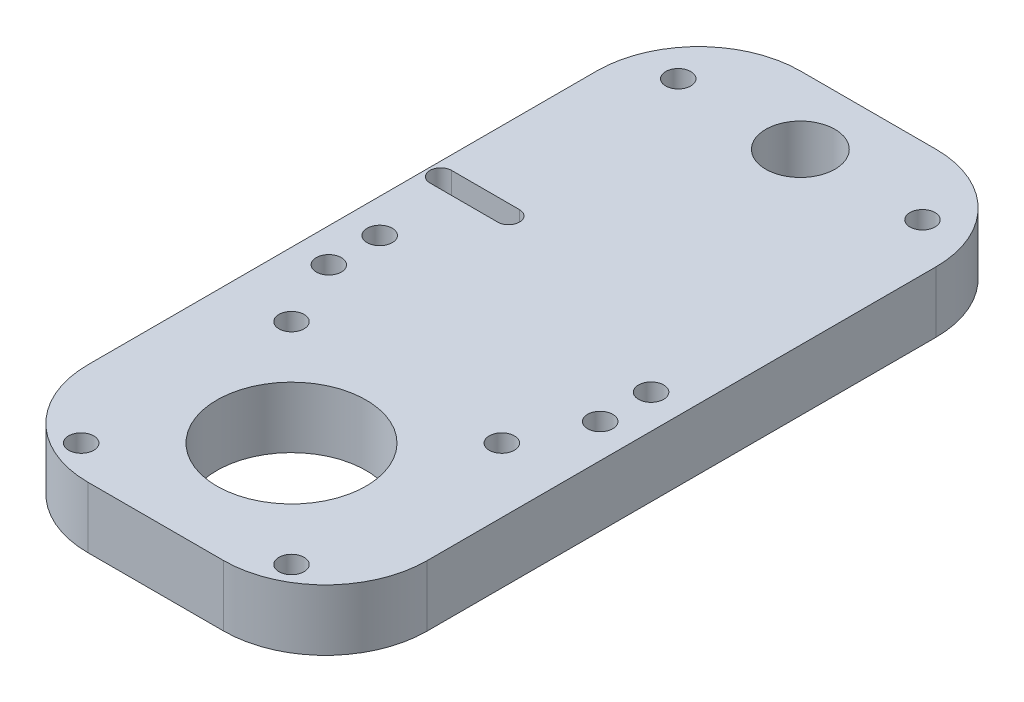
SolidWorks part; units mm, degrees
ref_plane "Front Plane" through (0, 0, 0) normal (0, 0, 1) x (1, 0, 0)
ref_plane "Top Plane" through (0, 0, 0) normal (0, 1, 0) x (1, 0, 0)
ref_plane "Right Plane" through (0, 0, 0) normal (1, 0, 0) x (0, 0, -1)
sketch "Sketch1" plane through (0, 0, 0) normal (0, 1, 0) x (1, 0, 0)
  line L1 (9.489, -12.4157) -> (59.489, -12.4157)
  line L2 (9.489, -12.4157) -> (9.489, 92.5843)
  line L3 (9.489, 92.5843) -> (59.489, 92.5843)
  line L4 (59.489, -12.4157) -> (59.489, 92.5843)
  dimension "D1" = 50
  dimension "D2" = 105
extrude "Boss-Extrude1" add sketch "Sketch1" along normal blind 9
sketch "Sketch2" plane through (0, 9, 0) normal (0, 1, 0) x (1, 0, 0)
  line L0 (9.489, -12.4157) -> (59.489, -12.4157) construction
  line L1 (34.489, 7.5843) -> (34.489, 80.959) construction
  line L6 (59.489, -12.4157) -> (59.489, 92.5843) construction
  line L7 (18.989, 23.0843) -> (18.989, -7.9157) construction
  line L8 (18.989, 23.0843) -> (49.989, -7.9157) construction
  line L9 (49.989, 23.0843) -> (18.989, -7.9157) construction
  line L10 (9.489, 92.5843) -> (9.489, -12.4157) construction
  line L11 (59.489, 40.0843) -> (-5.511, 40.0843) construction
  line L12 (21.489, 52.5843) -> (11.489, 52.5843) construction
  line L13 (21.489, 50.9843) -> (11.489, 50.9843)
  line L14 (21.489, 54.1843) -> (11.489, 54.1843)
  circle A4 centre (34.489, 7.5843) radius 11
  circle A6 centre (49.989, 23.0843) radius 1.85
  circle A7 centre (18.989, -7.9157) radius 1.85
  circle A8 centre (49.989, -7.9157) radius 1.85
  circle A9 centre (18.989, 23.0843) radius 1.85
  circle A12 centre (52.489, 82.5843) radius 1.85
  circle A13 centre (34.489, 82.5843) radius 5.1
  circle A14 centre (16.489, 82.5843) radius 1.85
  arc A15 (21.489, 50.9843) -> (21.489, 54.1843) centre (21.489, 52.5843) ccw
  arc A16 (11.489, 54.1843) -> (11.489, 50.9843) centre (11.489, 52.5843) ccw
  point P9 (16.489, 52.5843)
  dimension "D6" = 22
  dimension "D8" = 3.7
  dimension "D9" = 3.7
  dimension "D10" = 3.7
  dimension "D11" = 3.7
  dimension "D5" = 10.2
  dimension "D7" = 3.7
  dimension "D13" = 3.7
  dimension "D2" = 1.6
  dimension "D3" = 20
  dimension "D12" = 31
  dimension "D31" = 31
  dimension "D4" = 25
  dimension "D14" = 36
  dimension "D15" = 75
  dimension "D17" = 10
  dimension "D18" = 2
  dimension "D16" = 30
extrude "Cut-Extrude1" cut sketch "Sketch2" against normal blind 9
sketch "Sketch3" plane through (0, 9, 0) normal (0, 1, 0) x (1, 0, 0)
  line L0 (9.489, 92.5843) -> (9.489, -12.4157) construction
  line L5 (59.489, -12.4157) -> (59.489, 92.5843) construction
  line L6 (34.489, 18.5843) -> (34.489, 75.7406) construction
  line L7 (9.489, -12.4157) -> (59.489, -12.4157) construction
  circle A0 centre (14.489, 40.5843) radius 1.85
  circle A1 centre (54.489, 40.5843) radius 1.85
  circle A2 centre (54.489, 33.0843) radius 1.85
  circle A3 centre (14.489, 33.0843) radius 1.85
  circle A4 centre (34.489, 7.5843) radius 11 construction
  dimension "D1" = 3.7
  dimension "D2" = 3.7
  dimension "D3" = 3.7
  dimension "D4" = 3.7
  dimension "D5" = 7.5
  dimension "D8" = 5
  dimension "D9" = 5
  dimension "D6" = 53
extrude "Cut-Extrude4" cut sketch "Sketch3" against normal blind 10
fillet "Fillet1" radius 15 4 edges at (59.489, 4.5, 12.4157) (9.489, 4.5, 12.4157) (59.489, 4.5, -92.5843) (9.489, 4.5, -92.5843)
equation "\"D9@Sketch2\"=\"D8@Sketch2\""
equation "\"D10@Sketch2\"=\"D8@Sketch2\""
equation "\"D11@Sketch2\"=\"D8@Sketch2\""
equation "\"D2@Sketch3\"=\"D1@Sketch3\""
equation "\"D3@Sketch3\"=\"D1@Sketch3\""
equation "\"D4@Sketch3\"=\"D1@Sketch3\""
